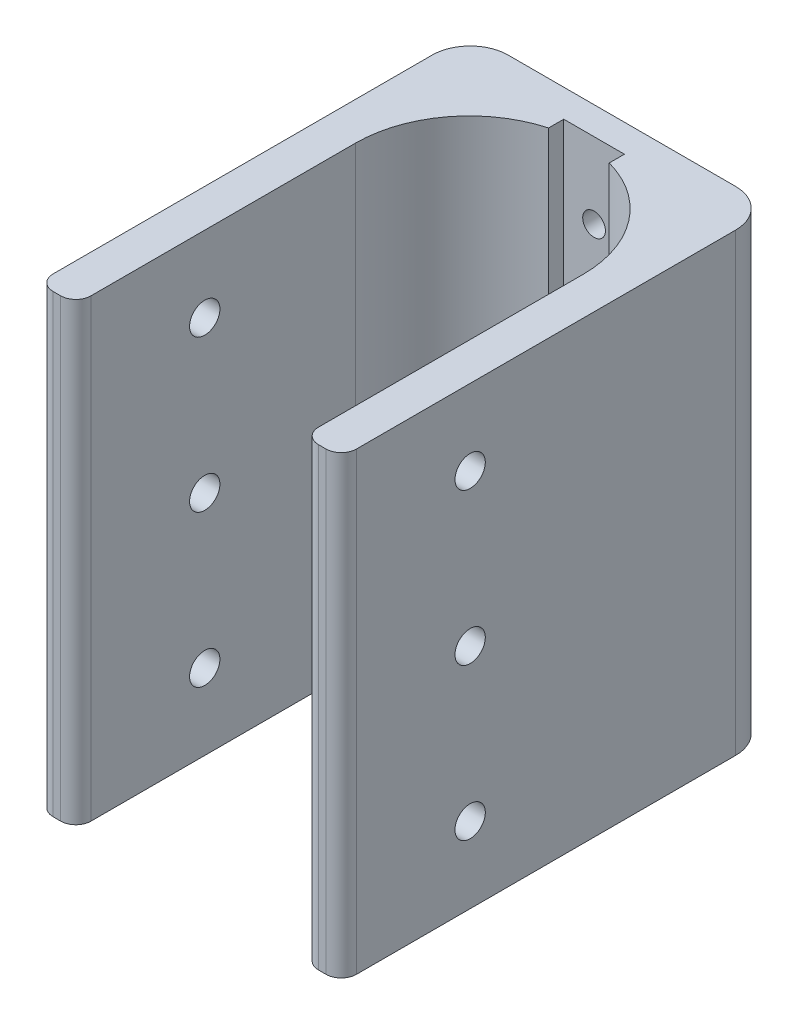
SolidWorks part; units mm, degrees
ref_plane "前视基准面" through (0, 0, 0) normal (0, 0, 1) x (1, 0, 0)
ref_plane "上视基准面" through (0, 0, 0) normal (0, 1, 0) x (1, 0, 0)
ref_plane "右视基准面" through (0, 0, 0) normal (1, 0, 0) x (0, 0, -1)
sketch "草图1" plane through (0, 0, 0) normal (0, 1, 0) x (1, 0, 0)
  line L0 (-33.2887, -40.9797) -> (-33.2887, -6.0931)
  line L2 (-3.2887, -6.0931) -> (-3.2887, -40.9797)
  line L3 (-1.2887, -42.9797) -> (-0.2887, -42.9797)
  line L7 (-36.2887, -42.9797) -> (-35.2887, -42.9797)
  line L8 (-18.2887, 8.9069) -> (-18.2887, -6.0931) construction
  line L9 (1.7113, 9.0203) -> (1.7113, -40.9797)
  line L10 (-3.2887, -6.0931) -> (-33.2887, -6.0931) construction
  line L11 (-18.2887, 12.0203) -> (-14.2887, 12.0203) construction
  line L12 (-14.2887, 12.0203) -> (-22.2887, 12.0203) construction
  line L13 (-22.2887, 12.0203) -> (-22.2887, 8.9069) construction
  line L14 (-22.2887, 8.9069) -> (-14.2887, 8.9069) construction
  line L15 (-14.2887, 8.9069) -> (-14.2887, 12.0203) construction
  line L16 (-38.2887, 9.0203) -> (-38.2887, -40.9797)
  line L19 (-14.2887, 10.3637) -> (-22.2887, 10.3637)
  line L21 (-14.2887, 10.3637) -> (-14.2887, 8.3637)
  line L23 (-33.2887, 14.0203) -> (-3.2887, 14.0203)
  line L25 (-22.2887, 10.3637) -> (-22.2887, 8.3637)
  arc A0 (-33.2887, -6.0931) -> (-22.2887, 8.3637) centre (-18.2887, -6.0931) cw
  arc A1 (-14.2887, 8.3637) -> (-3.2887, -6.0931) centre (-18.2887, -6.0931) cw
  arc A2 (1.7113, 9.0203) -> (-3.2887, 14.0203) centre (-3.2887, 9.0203) ccw
  arc A3 (-33.2887, 14.0203) -> (-38.2887, 9.0203) centre (-33.2887, 9.0203) ccw
  arc A4 (-38.2887, -40.9797) -> (-36.2887, -42.9797) centre (-36.2887, -40.9797) ccw
  arc A5 (-33.2887, -40.9797) -> (-35.2887, -42.9797) centre (-35.2887, -40.9797) cw
  arc A6 (-3.2887, -40.9797) -> (-1.2887, -42.9797) centre (-1.2887, -40.9797) ccw
  arc A7 (-0.2887, -42.9797) -> (1.7113, -40.9797) centre (-0.2887, -40.9797) ccw
  point P30 (-3.2887, -42.9797)
  point P33 (1.7113, -42.9797)
  dimension "D8" = 5
  dimension "D9" = 5
  dimension "D2" = 2
  dimension "D4" = 2
  dimension "D7" = 2
  dimension "D10" = 2
  dimension "D1" = 5
  dimension "D3" = 4
  dimension "D5" = 4
  dimension "D6" = 2
extrude "凸台-拉伸1" add sketch "草图1" along normal blind 60
sketch "草图2" plane through (0, 0, -10.3637) normal (0, 0, 1) x (1, 0, 0)
  line L0 (-18.2887, 60) -> (-18.2887, 0) construction
  line L1 (-14.2887, 60) -> (-22.2887, 60) construction
  line L2 (-14.2887, 0) -> (-22.2887, 0) construction
  line L3 (-18.2887, 0) -> (-18.2887, 30) construction
  line L4 (-18.2887, 30) -> (-18.2887, 50) construction
  line L5 (-18.2887, 50) -> (-18.2887, 30) construction
  line L6 (-18.2887, 30) -> (-18.2887, 10) construction
  circle A0 centre (-18.2887, 50) radius 1.5
  circle A1 centre (-18.2887, 30) radius 1.5
  circle A2 centre (-18.2887, 10) radius 1.5
extrude "切除-拉伸1" cut sketch "草图2" against normal blind 10
sketch "草图3" plane through (-38.2887, 0, 0) normal (-1, 0, 0) x (0, 0, 1)
  line L0 (42.9797, 60) -> (25.9797, 60)
  line L1 (-9.0203, 60) -> (40.9797, 60) construction
  line L2 (25.9797, 60) -> (25.9797, 0)
  line L3 (-9.0203, 0) -> (40.9797, 0) construction
  line L4 (25.9797, 0) -> (25.9797, 30)
  line L5 (25.9797, 30) -> (25.9797, 50)
  line L6 (25.9797, 50) -> (25.9797, 30)
  line L7 (25.9797, 30) -> (25.9797, 10)
  line L8 (-9.0203, 60) -> (-9.0203, 0) construction
  circle A0 centre (25.9797, 50) radius 2
  circle A1 centre (25.9797, 30) radius 2
  circle A2 centre (25.9797, 10) radius 2
  dimension "D1" = 20
  dimension "D2" = 35
extrude "切除-拉伸2" cut sketch "草图3" against normal through all contours A2 | A1 | A0
